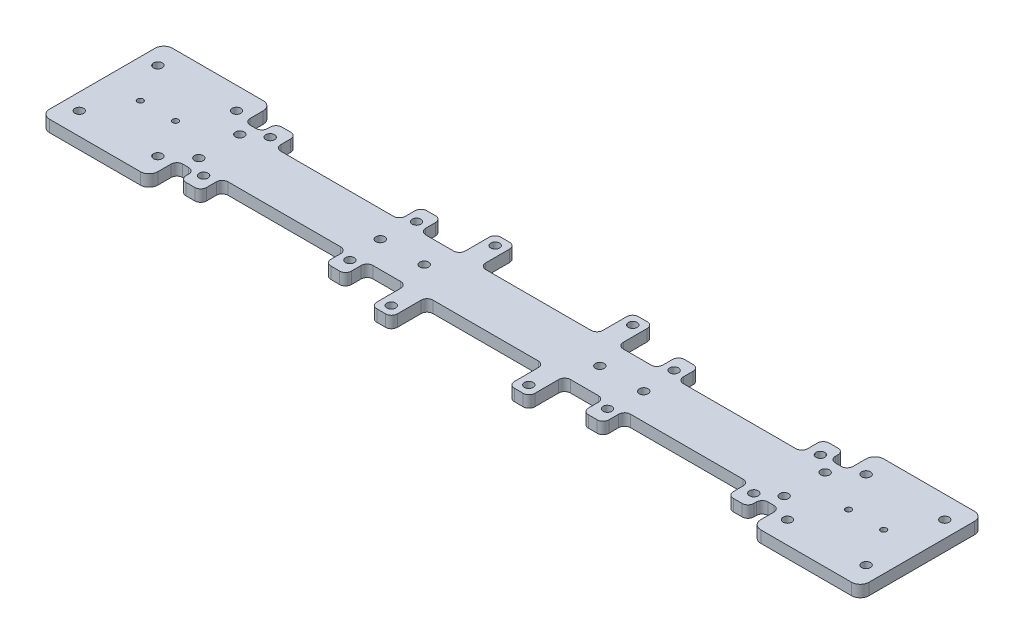
SolidWorks part; units mm, degrees
ref_plane "前视基准面" through (0, 0, 0) normal (0, 0, 1) x (1, 0, 0)
ref_plane "上视基准面" through (0, 0, 0) normal (0, 1, 0) x (1, 0, 0)
ref_plane "右视基准面" through (0, 0, 0) normal (1, 0, 0) x (0, 0, -1)
sketch "草图1" plane through (0, 0, 0) normal (0, 1, 0) x (1, 0, 0)
  line L1 (140, -21) -> (-140, -21)
  line L2 (140, -21) -> (140, 21)
  line L3 (140, 21) -> (-140, 21)
  line L4 (-140, -21) -> (-140, 21)
  line L5 (140, -21) -> (-140, 21) construction
  line L6 (140, 21) -> (-140, -21) construction
  point P0 (0, 0)
extrude "凸台-拉伸1" add sketch "草图1" along normal blind 4
sketch "草图2" plane through (0, 4, 0) normal (0, 1, 0) x (1, 0, 0)
  line L0 (-140, 0) -> (-121, 0) construction
  line L1 (-140, 21) -> (-140, -21) construction
  line L2 (-121, 0) -> (-134.435, 13.435) construction
  circle A0 centre (-121, 0) radius 19 construction
  circle A1 centre (-134.435, 13.435) radius 1.5
  circle A2 centre (-107.565, 13.435) radius 1.5
  circle A3 centre (-107.565, -13.435) radius 1.5
  circle A4 centre (-134.435, -13.435) radius 1.5
  circle A5 centre (-121, 0) radius 6 construction
  circle A6 centre (-127, 0) radius 1
  circle A7 centre (-115, 0) radius 1
  point P17 (-121, 0)
  dimension "D2" = 4
  dimension "D1" = 19
extrude "切除-拉伸1" cut sketch "草图2" against normal through all
sketch "草图4" plane through (0, 4, 0) normal (0, 1, 0) x (1, 0, 0)
  line L0 (-140, 0) -> (-100, 0) construction
  line L1 (-140, 21) -> (-140, -21) construction
  circle A0 centre (-100, 0) radius 7 construction
  circle A7 centre (-100, 7) radius 1.5
  circle A8 centre (-100, -7) radius 1.5
  dimension "D1" = 40
extrude "切除-拉伸2" cut sketch "草图4" against normal through all
sketch "草图5" plane through (0, 4, 0) normal (0, 1, 0) x (1, 0, 0)
  line L0 (140, 21) -> (-140, 21) construction
  line L1 (90, 32.9741) -> (-90, 32.9741)
  line L2 (90, 32.9741) -> (90, 9.0259)
  line L3 (90, 9.0259) -> (-90, 9.0259)
  line L4 (-90, 32.9741) -> (-90, 9.0259)
  line L5 (90, 32.9741) -> (-90, 9.0259) construction
  line L6 (90, 9.0259) -> (-90, 32.9741) construction
  line L7 (-140, 21) -> (-140, -21) construction
  point P0 (0, 21)
  dimension "D1" = 50
extrude "切除-拉伸3" cut sketch "草图5" against normal through all
sketch "草图6" plane through (0, 4, 0) normal (0, 1, 0) x (1, 0, 0)
  line L0 (-140, 0) -> (-51.6897, 0) construction
  line L1 (-140, 21) -> (-140, -21) construction
  line L2 (-94, 0) -> (-94, 11.375) construction
  circle A0 centre (-94, 11.375) radius 1.5
  circle A1 centre (-94, -11.375) radius 1.5
  dimension "D2" = 46
  dimension "D1" = 11.375
extrude "切除-拉伸4" cut sketch "草图6" against normal through all
sketch "草图7" plane through (0, 4, 0) normal (0, 1, 0) x (1, 0, 0)
  line L5 (-94, 11.375) -> (-44, 11.375) construction
  line L6 (0, -2.2) -> (0, 2.2) construction
  line L7 (-40.5, 16.375) -> (-47.5, 16.375)
  line L8 (-40.5, 16.375) -> (-40.5, 6.375)
  line L9 (-40.5, 6.375) -> (-47.5, 6.375)
  line L10 (-47.5, 16.375) -> (-47.5, 6.375)
  line L11 (-40.5, 16.375) -> (-47.5, 6.375) construction
  line L12 (-40.5, 6.375) -> (-47.5, 16.375) construction
  line L13 (40.5, 6.375) -> (47.5, 16.375) construction
  line L14 (40.5, 16.375) -> (47.5, 6.375) construction
  line L15 (47.5, 16.375) -> (47.5, 6.375)
  line L16 (40.5, 6.375) -> (47.5, 6.375)
  line L17 (40.5, 16.375) -> (40.5, 6.375)
  line L18 (40.5, 16.375) -> (47.5, 16.375)
  circle A1 centre (-44, 11.375) radius 1.5
  circle A2 centre (44, 11.375) radius 1.5
  dimension "D1" = 50
extrude "凸台-拉伸2" add sketch "草图7" against normal up to surface (4 mm away) up to face at (-94, 0, -9.875)
sketch "草图9" plane through (0, 4, 0) normal (0, 1, 0) x (1, 0, 0)
  line L0 (0, 0) -> (0, 17.75) construction
  line L1 (0, 17.75) -> (23.5, 17.75) construction
  line L2 (-40.5, 9.0259) -> (40.5, 9.0259) construction
  line L3 (27, -3.1359) -> (20, -3.1359)
  line L4 (27, -3.1359) -> (27, 21.1877)
  line L5 (27, 21.1877) -> (20, 21.1877)
  line L6 (20, -3.1359) -> (20, 21.1877)
  line L7 (27, -3.1359) -> (20, 21.1877) construction
  line L8 (27, 21.1877) -> (20, -3.1359) construction
  line L9 (-27, 21.1877) -> (-20, -3.1359) construction
  line L10 (-27, -3.1359) -> (-20, 21.1877) construction
  line L11 (-20, -3.1359) -> (-20, 21.1877)
  line L12 (-27, 21.1877) -> (-20, 21.1877)
  line L13 (-27, -3.1359) -> (-27, 21.1877)
  line L14 (-27, -3.1359) -> (-20, -3.1359)
  circle A0 centre (23.5, 17.75) radius 1.5
  circle A1 centre (-23.5, 17.75) radius 1.5
  point P1 (23.5, 9.0259)
  point P19 (-23.5, 9.0259)
  dimension "D2" = 17.75
  dimension "D1" = 23.5
extrude "凸台-拉伸3" add sketch "草图9" against normal up to surface (4 mm away) up to face at (0, 0, -10.1035)
sketch "草图12" plane through (0, 4, 0) normal (0, 1, 0) x (1, 0, 0)
  line L0 (-44, 16.375) -> (-101.6623, 16.375) construction
  line L1 (-40.5, 16.375) -> (-47.5, 16.375) construction
  line L2 (-90, 21) -> (-90, 9.0259) construction
  line L3 (-90, 21) -> (-90, 9.0259) construction
  line L5 (-90, 16.375) -> (-98.3215, 16.375)
  line L6 (-90, 16.375) -> (-90, 25.4216)
  line L7 (-90, 25.4216) -> (-98.3215, 25.4216)
  line L8 (-98.3215, 16.375) -> (-98.3215, 25.4216)
extrude "切除-拉伸8" cut sketch "草图12" against normal through all
sketch "草图11" plane through (0, 4, 0) normal (0, 1, 0) x (1, 0, 0)
  line L0 (-100, 7) -> (-100, 21) construction
  line L7 (-97, 22.2693) -> (-103, 22.2693)
  line L8 (-97, 22.2693) -> (-97, 11.5219)
  line L9 (-97, 11.5219) -> (-103, 11.5219)
  line L10 (-103, 22.2693) -> (-103, 11.5219)
  line L11 (-97, 22.2693) -> (-103, 11.5219) construction
  line L12 (-97, 11.5219) -> (-103, 22.2693) construction
  point P6 (-100, 16.8956)
extrude "切除-拉伸7" cut sketch "草图11" against normal through all
mirror "镜向4" about plane through (0, 0, 0) normal (1, 0, 0) of "切除-拉伸8", "切除-拉伸7"
mirror "镜向2" about plane through (0, 0, 0) normal (0, 0, 1) of "镜向4", "切除-拉伸3", "切除-拉伸8", "切除-拉伸7"
fillet "圆角1" radius 3 4 edges at (-140, 2, 21) (-140, 2, -21) (-103, 2, -21) (-103, 2, 21)
mirror "镜向1" about plane through (0, 0, 0) normal (1, 0, 0) of "切除-拉伸4", "切除-拉伸2", "切除-拉伸1", "圆角1"
fillet "圆角3" radius 2 8 edges at (47.5, 2, -16.375) (40.5, 2, -16.375) (27, 2, -21.1877) (-20, 2, -21.1877) (-27, 2, -21.1877) (-40.5, 2, -16.375) (-47.5, 2, -16.375) (20, 2, -21.1877)
mirror "镜向3" about plane through (0, 0, 0) normal (0, 0, 1) of "圆角3", "凸台-拉伸3", "凸台-拉伸2"
sketch "草图10" plane through (0, 4, 0) normal (0, 1, 0) x (1, 0, 0)
  line L0 (0, 9.0259) -> (0, -19.4645) construction
  line L1 (-20, 9.0259) -> (20, 9.0259) construction
  circle A0 centre (0, 0) radius 30 construction
  circle A1 centre (-30, 0) radius 1.5
  circle A2 centre (0, 0) radius 45 construction
  circle A3 centre (-45, 0) radius 1.5
  circle A4 centre (30, 0) radius 1.5
  circle A5 centre (45, 0) radius 1.5
extrude "切除-拉伸6" cut sketch "草图10" against normal through all
fillet "圆角6" radius 2 8 edges at (97, 2, -16.375) (90, 2, -16.375) (97, 2, 16.375) (90, 2, 16.375) (-97, 2, 16.375) (-90, 2, 16.375) (-90, 2, -16.375) (-97, 2, -16.375)
fillet "圆角7" radius 2 12 edges at (-90, 2, 9.0259) (-90, 2, -9.0259) (-97, 2, 11.5219) (-103, 2, 11.5219) (-103, 2, -11.5219) (-97, 2, -11.5219) (103, 2, 11.5219) (97, 2, 11.5219) (90, 2, 9.0259) (90, 2, -9.0259) (97, 2, -11.5219) (103, 2, -11.5219)
fillet "圆角8" radius 2 8 edges at (47.5, 2, -9.0259) (40.5, 2, -9.0259) (27, 2, -9.0259) (20, 2, -9.0259) (-20, 2, -9.0259) (-27, 2, -9.0259) (-40.5, 2, -9.0259) (-47.5, 2, -9.0259)
fillet "圆角9" radius 2 8 edges at (40.5, 2, 9.0259) (47.5, 2, 9.0259) (27, 2, 9.0259) (20, 2, 9.0259) (-20, 2, 9.0259) (-27, 2, 9.0259) (-40.5, 2, 9.0259) (-47.5, 2, 9.0259)
